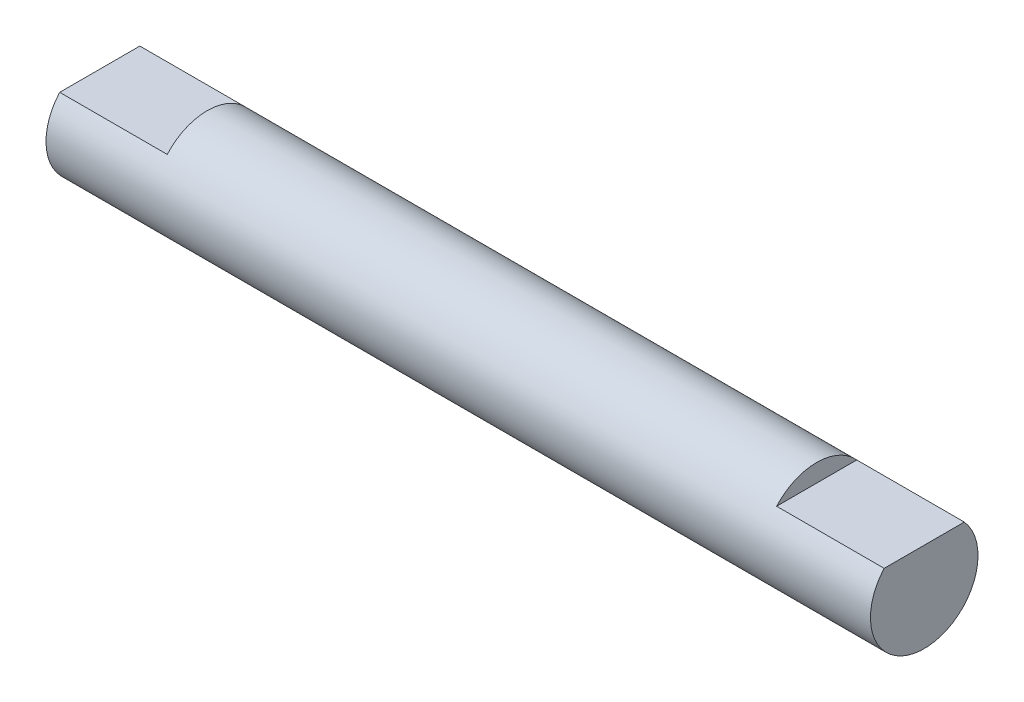
SolidWorks part; units mm, degrees
ref_plane "Front Plane" through (0, 0, 0) normal (0, 0, 1) x (1, 0, 0)
ref_plane "Top Plane" through (0, 0, 0) normal (0, 1, 0) x (1, 0, 0)
ref_plane "Right Plane" through (0, 0, 0) normal (1, 0, 0) x (0, 0, -1)
sketch "Sketch2" plane through (0, 0, 0) normal (0, 0, 1) x (1, 0, 0)
  line L0 (0, 0) -> (46, 0)
  line L1 (46, 0) -> (46, -3)
  line L2 (46, -3) -> (0, -3)
  line L3 (0, -3) -> (0, 0)
  point P3 (0, 0)
  dimension "D1" = 46
  dimension "D2" = 3
revolve "Revolve1" add sketch "Sketch2" angle 360 about L0
sketch "Sketch3" plane through (46, 0, 0) normal (1, 0, 0) x (0, 0, -1)
  line L0 (-2.2361, 2) -> (2.2361, 2)
  circle A1 centre (0, 0) radius 3
  arc A2 (2.2361, 2) -> (-2.2361, 2) centre (0, 0) ccw
  dimension "D2" = 2
  dimension "D1" = 0
extrude "Cut-Extrude1" cut sketch "Sketch3" against normal blind 6
sketch "Sketch4" plane through (0, 0, 0) normal (-1, 0, 0) x (0, 0, 1)
  line L0 (-2.2361, 2) -> (2.2361, 2)
  circle A1 centre (0, 0) radius 3
  arc A2 (2.2361, 2) -> (-2.2361, 2) centre (0, 0) ccw
  dimension "D2" = 2
  dimension "D1" = 0
extrude "Cut-Extrude2" cut sketch "Sketch4" against normal blind 6
